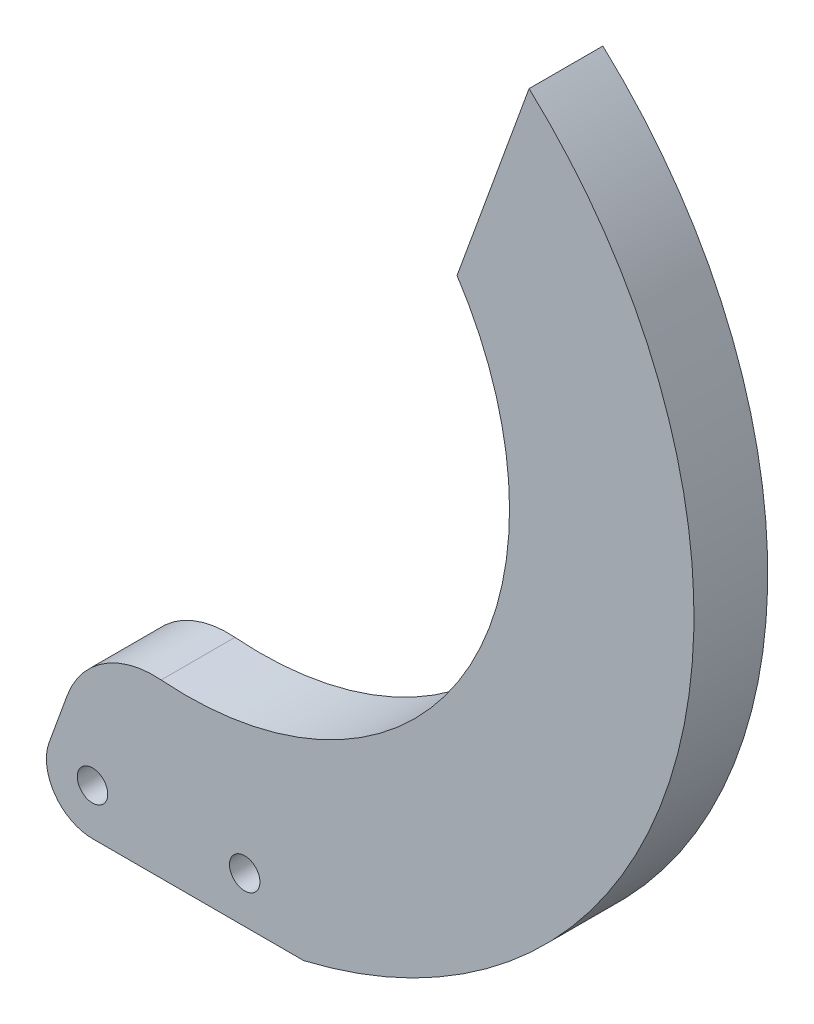
SolidWorks part; units mm, degrees
ref_plane "前基準面" through (0, 0, 0) normal (0, 0, 1) x (1, 0, 0)
ref_plane "上基準面" through (0, 0, 0) normal (0, 1, 0) x (1, 0, 0)
ref_plane "右基準面" through (0, 0, 0) normal (1, 0, 0) x (0, 0, -1)
sketch "草圖1" plane through (0, 0, 0) normal (0, 0, 1) x (1, 0, 0)
  line L0 (0, -5) -> (22.8963, -5)
  line L1 (47.3346, 89.1031) -> (39.5253, 67.6471)
  line L2 (-4.6985, 1.7101) -> (0.1387, 15)
  line L3 (10.2152, 48.5181) -> (2.4058, 27.0621) construction
  line L4 (0, 0) -> (45.7917, 0) construction
  line L5 (45.7917, 0) -> (0, 0) construction
  line L6 (0, 0) -> (16.5, 0) construction
  line L7 (10.2152, 48.5181) -> (-2.3417, 53.0884) construction
  circle A0 centre (0, 0) radius 1.65
  arc A1 (-4.6985, 1.7101) -> (0, -5) centre (0, 0) ccw
  arc A2 (0.1387, 15) -> (39.5253, 67.6471) centre (10.2152, 48.5181) ccw
  arc A3 (22.8963, -5) -> (47.3346, 89.1031) centre (10.2152, 48.5181) ccw
  circle A4 centre (16.5, 0) radius 1.65
  dimension "D2" = 35
  dimension "D6" = 3.3
  dimension "D7" = 5
  dimension "D8" = 20
  dimension "D4" = 5
  dimension "D5" = 1.9951
  dimension "D9" = 55
  dimension "D1" = 70
  dimension "D3" = 16.5
  dimension "D10" = 42
extrude "填料-伸長1" add sketch "草圖1" along normal blind 8
fillet "圓角1" radius 10 1 edges at (0.1387, 15, 4)
sketch "草圖2" plane through (0, 0, 0) normal (0, 0, -1) x (-1, 0, 0)
  circle A0 centre (0, 0) radius 4
  dimension "D1" = 8
extrude "除料-伸長1" cut sketch "草圖2" against normal blind 3
